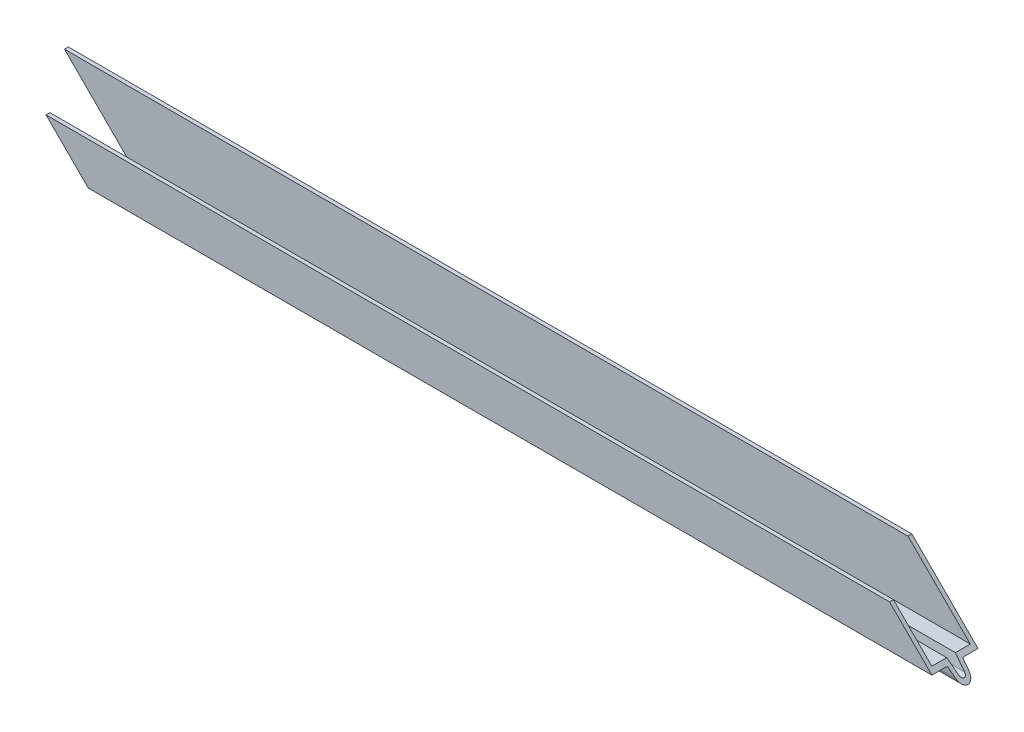
SolidWorks part; units mm, degrees
material "6063-O"
ref_plane "Front Plane" through (0, 0, 0) normal (0, 0, 1) x (1, 0, 0)
ref_plane "Top Plane" through (0, 0, 0) normal (0, 1, 0) x (1, 0, 0)
ref_plane "Right Plane" through (0, 0, 0) normal (1, 0, 0) x (0, 0, -1)
other "Configuration Table"
sketch "Sketch1" plane through (0, 0, 0) normal (1, 0, 0) x (0, 0, -1)
  line L0 (7.62, 0) -> (7.62, -21.844)
  line L1 (7.62, -21.844) -> (2.54, -21.844)
  line L2 (-2.54, -21.844) -> (-2.2022, -24.2477)
  line L3 (2.2022, -24.2477) -> (2.54, -21.844)
  line L4 (-2.54, -21.844) -> (-7.62, -21.844)
  line L5 (-7.62, -21.844) -> (-7.62, -7.874)
  line L6 (6.35, 0) -> (6.35, -20.574)
  line L7 (6.35, -20.574) -> (1.436, -20.574)
  line L8 (0.9445, -24.0709) -> (1.436, -20.574)
  line L9 (-1.436, -20.574) -> (-0.9445, -24.0709)
  line L10 (-1.436, -20.574) -> (-6.35, -20.574)
  line L11 (-6.35, -20.574) -> (-6.35, -7.874)
  line L12 (7.62, 0) -> (6.35, 0)
  line L13 (-7.62, -7.874) -> (-6.35, -7.874)
  line L14 (0, 0) -> (0, -30.4009) construction
  arc A0 (-2.2022, -24.2477) -> (2.2022, -24.2477) centre (0, -23.9382) ccw
  arc A1 (-0.9445, -24.0709) -> (0.9445, -24.0709) centre (0, -23.9382) ccw
  dimension "D1" = 15.24
  dimension "D2" = 4.318
  dimension "D3" = 21.844
  dimension "D4" = 13.97
  dimension "D5" = 12.7
  dimension "D6" = 82
  dimension "D7" = 5.08
extrude "Boss-Extrude1" add sketch "Sketch1" along normal mid plane 304.8
sketch "Sketch4" plane through (0, 0, 0) normal (0, 1, 0) x (1, 0, 0)
  line L0 (-152.4, 7.62) -> (-137.16, -7.62)
  line L1 (152.4, -7.62) -> (-152.4, -7.62) construction
  line L2 (-137.16, -7.62) -> (-152.4, -7.62)
  line L3 (-152.4, -7.62) -> (-152.4, 7.62)
extrude "Cut-Top-Left-Front" [suppressed] cut sketch "Sketch4" against normal through all
sketch "Sketch12" plane through (0, 0, 7.62) normal (0, 0, 1) x (1, 0, 0)
  line L0 (-152.4, 0) -> (-126.238, -26.162)
  line L1 (-152.4, -26.162) -> (152.4, -26.162) construction
  line L2 (-126.238, -26.162) -> (-152.4, -26.162)
  line L3 (-152.4, -26.162) -> (-152.4, 0)
extrude "Cut-Front-Left-Bottom" cut sketch "Sketch12" against normal through all
sketch "Sketch9" plane through (0, 0, 7.62) normal (0, 0, 1) x (1, 0, 0)
  line L0 (-152.4, -26.162) -> (-126.238, 0)
  line L1 (152.4, 0) -> (-152.4, 0) construction
  line L2 (-126.238, 0) -> (-152.4, 0)
  line L3 (-152.4, 0) -> (-152.4, -26.162)
extrude "Cut-Front-Left-Top" [suppressed] cut sketch "Sketch9" against normal through all
sketch "Sketch7" plane through (0, 0, 7.62) normal (0, 0, 1) x (1, 0, 0)
  line L0 (152.4, -26.162) -> (126.238, 0)
  line L2 (126.238, 0) -> (152.4, 0)
  line L4 (152.4, 0) -> (152.4, -26.162)
  line L5 (152.4, -7.874) -> (152.4, -21.844) construction
  line L6 (152.4, 0) -> (-152.4, 0) construction
extrude "Cut-Front-Right-Top" cut sketch "Sketch7" against normal through all
sketch "Sketch2" plane through (0, 0, 0) normal (0, 1, 0) x (1, 0, 0)
  line L0 (152.4, 7.62) -> (137.16, -7.62)
  line L1 (134.112, -7.62) -> (-144.526, -7.62) construction
  line L2 (137.16, -7.62) -> (152.4, -7.62)
  line L3 (152.4, -7.62) -> (152.4, 7.62)
extrude "Cut-Top-Right-Front" [suppressed] cut sketch "Sketch2" against normal through all
sketch "Sketch11" plane through (0, 0, 7.62) normal (0, 0, 1) x (1, 0, 0)
  line L0 (152.4, 0) -> (126.238, -26.162)
  line L1 (-126.238, -26.162) -> (152.4, -26.162) construction
  line L2 (126.238, -26.162) -> (152.4, -26.162)
  line L3 (152.4, -26.162) -> (152.4, 0)
extrude "Cut-Front-Right-Bottom" [suppressed] cut sketch "Sketch11" against normal through all
